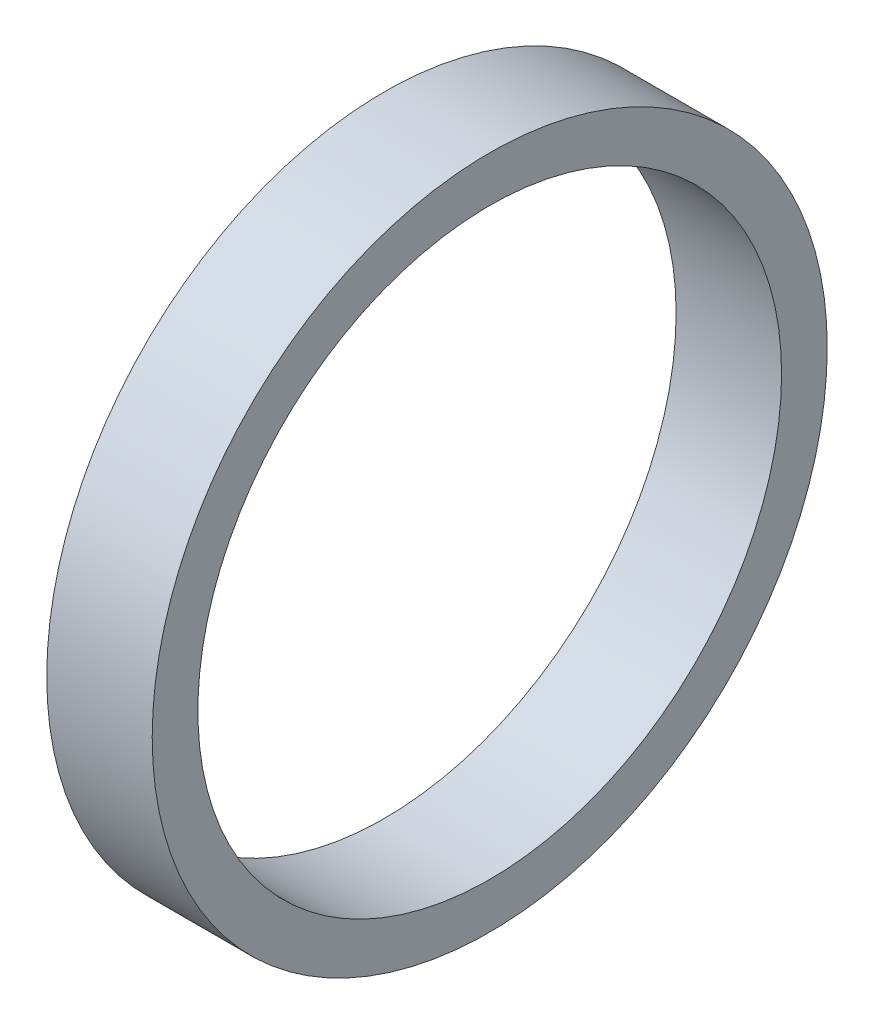
SolidWorks part; units mm, degrees
material "PE High Density"
ref_plane "Front Plane" through (0, 0, 0) normal (0, 0, 1) x (1, 0, 0)
ref_plane "Top Plane" through (0, 0, 0) normal (0, 1, 0) x (1, 0, 0)
ref_plane "Right Plane" through (0, 0, 0) normal (1, 0, 0) x (0, 0, -1)
sketch "Sketch1" plane through (0, 0, 0) normal (1, 0, 0) x (0, 0, -1)
  circle A0 centre (0, 0) radius 17.575
  circle A1 centre (0, 0) radius 20.325
  dimension "D1" = 35.15
  dimension "D2" = 2.75
extrude "Boss-Extrude1" add sketch "Sketch1" along normal blind 6.35
